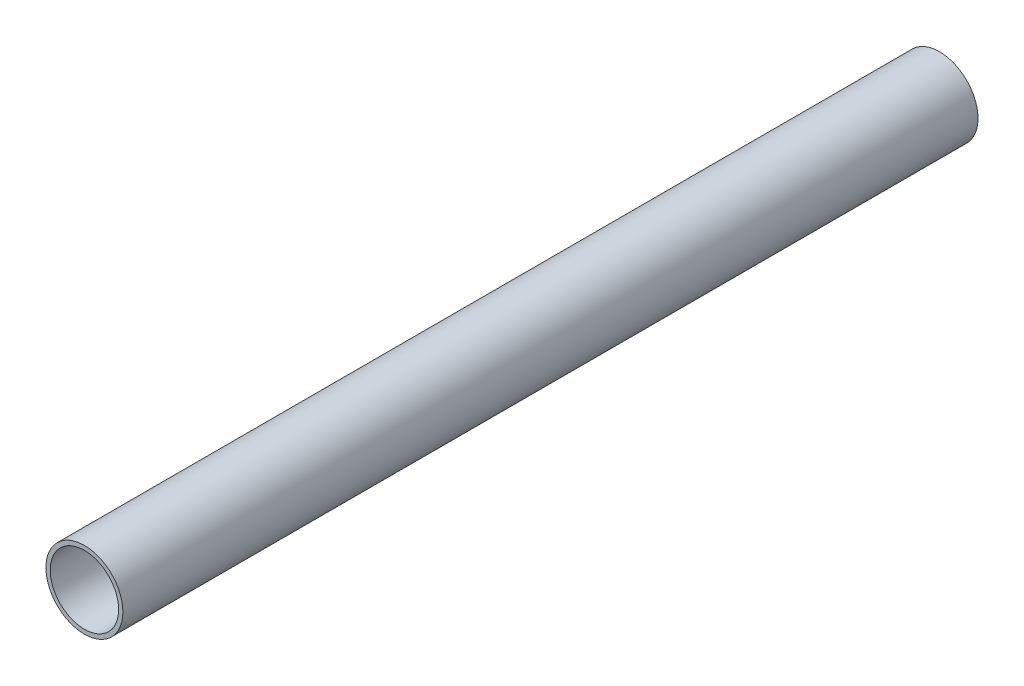
SolidWorks part; units mm, degrees
ref_plane "Front Plane" through (0, 0, 0) normal (0, 0, 1) x (1, 0, 0)
ref_plane "Top Plane" through (0, 0, 0) normal (0, 1, 0) x (1, 0, 0)
ref_plane "Right Plane" through (0, 0, 0) normal (1, 0, 0) x (0, 0, -1)
sketch "Sketch1" plane through (0, 0, 0) normal (0, 0, 1) x (1, 0, 0)
  circle A0 centre (0, 0) radius 2
  circle A1 centre (0, 0) radius 2.25
  dimension "D1" = 4
  dimension "D2" = 4.5
extrude "Boss-Extrude1" add sketch "Sketch1" along normal blind 50
